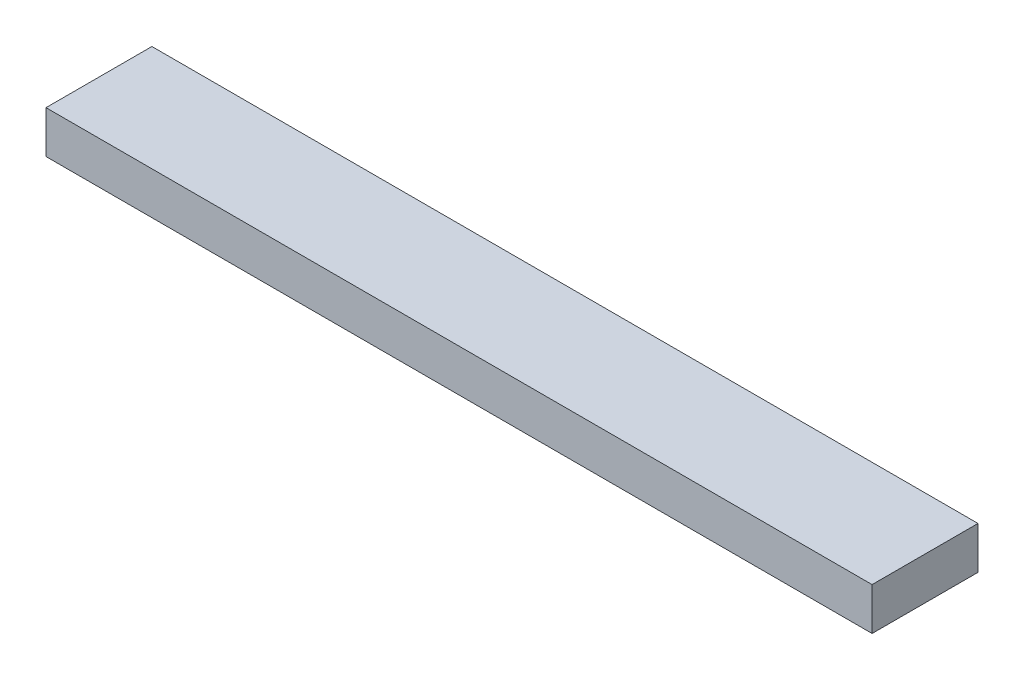
SolidWorks part; units mm, degrees
material "1023 Carbon Steel Sheet (SS)"
ref_plane "Front Plane" through (0, 0, 0) normal (0, 0, 1) x (1, 0, 0)
ref_plane "Top Plane" through (0, 0, 0) normal (0, 1, 0) x (1, 0, 0)
ref_plane "Right Plane" through (0, 0, 0) normal (1, 0, 0) x (0, 0, -1)
sketch "Sketch1" plane through (0, 0, 0) normal (1, 0, 0) x (0, 0, -1)
  line L1 (0, 0) -> (127, 0)
  line L2 (0, 0) -> (0, 50.8)
  line L3 (0, 50.8) -> (127, 50.8)
  line L4 (127, 0) -> (127, 50.8)
  dimension "D1" = 50.8
  dimension "D2" = 127
extrude "Boss-Extrude1" add sketch "Sketch1" along normal blind 990.6
